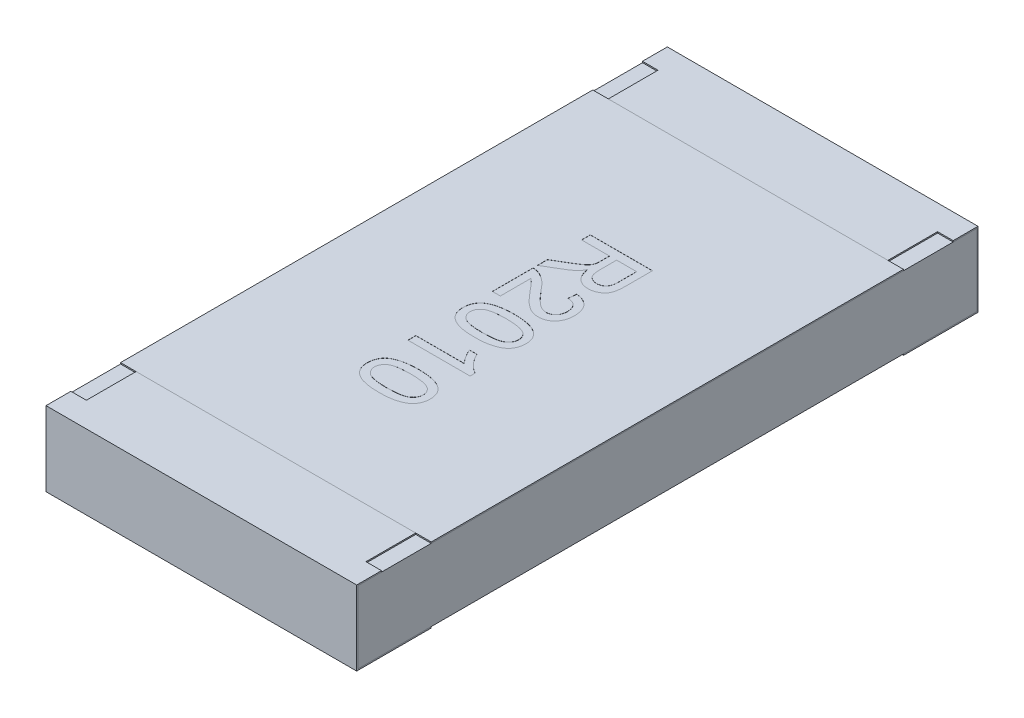
SolidWorks part; units mm, degrees
ref_plane "Front Plane" through (0, 0, 0) normal (0, 0, 1) x (1, 0, 0)
ref_plane "Top Plane" through (0, 0, 0) normal (0, 1, 0) x (1, 0, 0)
ref_plane "Right Plane" through (0, 0, 0) normal (1, 0, 0) x (0, 0, -1)
sketch "Sketch4" plane through (0, 0, 0) normal (1, 0, 0) x (0, 0, -1)
  line L0 (0, 0.1169) -> (0, -0.0721) construction
  line L1 (-2.5, 0) -> (0.3788, 0) construction
  line L2 (-2.5, 0.3) -> (-2.5, -0.3)
  line L3 (-2.5, -0.3) -> (-1.9, -0.3)
  line L4 (-1.9, 0.3) -> (-1.9, 0.29)
  line L5 (-1.9, 0.29) -> (-2.49, 0.29)
  line L6 (-2.49, 0.29) -> (-2.49, -0.29)
  line L7 (-2.49, -0.29) -> (-1.9, -0.29)
  line L8 (-1.9, -0.29) -> (-1.9, -0.3)
  line L9 (-1.9, 0.3) -> (-2.5, 0.3)
  line L10 (1.9, 0.3) -> (2.5, 0.3)
  line L11 (1.9, -0.29) -> (1.9, -0.3)
  line L12 (2.49, -0.29) -> (1.9, -0.29)
  line L13 (2.49, 0.29) -> (2.49, -0.29)
  line L14 (1.9, 0.29) -> (2.49, 0.29)
  line L15 (1.9, 0.3) -> (1.9, 0.29)
  line L16 (2.5, -0.3) -> (1.9, -0.3)
  line L17 (2.5, 0.3) -> (2.5, -0.3)
  dimension "LENGTH" = 2.5
  dimension "HEIGHT" = 0.6
  dimension "END CAP TOP LENGTH" = 0.6
  dimension "END CAP BOTTOM LENGTH" = 0.6
  dimension "D5" = 0.01
  dimension "D6" = 0.01
extrude "Boss-Extrude2" add sketch "Sketch4" along normal mid plane 2.5
sketch "Sketch5" plane through (0, 0, 0) normal (1, 0, 0) x (0, 0, -1)
  line L1 (-2.49, 0.29) -> (2.49, 0.29)
  line L2 (-2.49, 0.29) -> (-2.49, -0.29)
  line L3 (-2.49, -0.29) -> (2.49, -0.29)
  line L4 (2.49, 0.29) -> (2.49, -0.29)
extrude "Boss-Extrude3" add sketch "Sketch5" along normal up to surface and the other way up to surface separate body
sketch "Sketch6" plane through (0, 0.3, 0) normal (0, 1, 0) x (1, 0, 0)
  line L0 (-1.25, 2.5) -> (-1.25, 1.9) construction
  line L1 (-1.25, 2.3) -> (-1.125, 2.3)
  line L2 (-1.25, 2.3) -> (-1.25, 1.9)
  line L3 (-1.25, 1.9) -> (-1.125, 1.9)
  line L4 (-1.125, 2.3) -> (-1.125, 1.9)
  line L5 (1.25, 1.9) -> (-1.25, 1.9) construction
  line L6 (0, 0.0345) -> (0, -0.0345) construction
  line L7 (-0.0325, 0) -> (0.03, 0) construction
  line L8 (1.25, 2.3) -> (1.25, 1.9)
  line L9 (1.25, 1.9) -> (1.125, 1.9)
  line L10 (1.125, 2.3) -> (1.125, 1.9)
  line L11 (1.25, 2.3) -> (1.125, 2.3)
  line L12 (1.25, -2.3) -> (1.125, -2.3)
  line L13 (1.25, -2.3) -> (1.25, -1.9)
  line L14 (1.25, -1.9) -> (1.125, -1.9)
  line L15 (1.125, -2.3) -> (1.125, -1.9)
  line L16 (-1.25, -2.3) -> (-1.125, -2.3)
  line L17 (-1.25, -2.3) -> (-1.25, -1.9)
  line L18 (-1.25, -1.9) -> (-1.125, -1.9)
  line L19 (-1.125, -2.3) -> (-1.125, -1.9)
  dimension "TOP CUT WIDTH" = 0.125
  dimension "TOP CUT LENGTH" = 0.4
extrude "Cut-Extrude1" cut sketch "Sketch6" against normal up to surface (0.01 mm away) up to face at (0, 0.29, 0)
sketch "Sketch7" plane through (0, 0.29, 0) normal (0, 1, 0) x (1, 0, 0)
  line L1 (-1.25, 1.9) -> (1.25, 1.9)
  line L2 (-1.25, 1.9) -> (-1.25, -1.9)
  line L3 (-1.25, -1.9) -> (1.25, -1.9)
  line L4 (1.25, 1.9) -> (1.25, -1.9)
  line L5 (1.125, -1.9) -> (-1.125, -1.9) construction
  line L6 (1.125, 1.9) -> (-1.125, 1.9) construction
  line L7 (-1.25, -2.49) -> (-1.25, 2.49) construction
  line L8 (1.25, 2.49) -> (1.25, -2.49) construction
extrude "Boss-Extrude4" add sketch "Sketch7" along normal up to surface (0.01 mm away) separate body up to face at (0, 0.3, -2.25)
sketch "Sketch15" plane through (0, 0.3, 0) normal (0, 1, 0) x (1, 0, 0)
  line L0 (-0.25, 0.9382) -> (-0.25, -0.9382) construction
  line L1 (0, 0) -> (-0.25, 0) construction
  text T0 "R2010" font "Arial" height 0.5
  dimension "D1" = 0.25
extrude "TEXT2010" cut sketch "Sketch15" against normal blind 0.001
